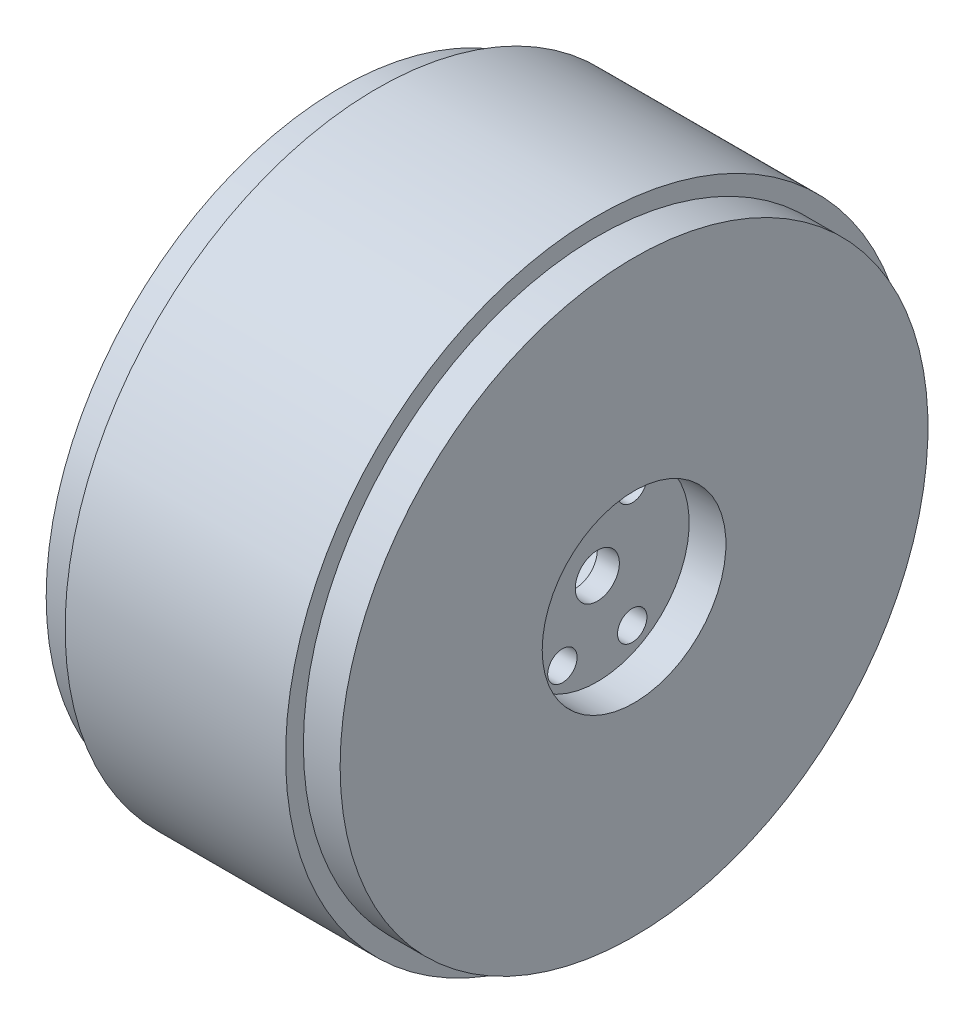
SolidWorks part; units mm, degrees
ref_plane "Plan de face" through (0, 0, 0) normal (0, 0, 1) x (1, 0, 0)
ref_plane "Plan de dessus" through (0, 0, 0) normal (0, 1, 0) x (1, 0, 0)
ref_plane "Plan de droite" through (0, 0, 0) normal (1, 0, 0) x (0, 0, -1)
sketch "Esquisse1" plane through (0, 0, 0) normal (0, 0, 1) x (1, 0, 0)
  line L0 (-49.6445, 0) -> (53.9199, 0) construction
  line L1 (0, 34) -> (0, 0)
  line L2 (0, 34) -> (-32, 34)
  line L3 (-32, 34) -> (-32, 40)
  line L4 (-32, 40) -> (-27, 40)
  line L5 (-27, 40) -> (-27, 39)
  line L6 (-27, 39) -> (3, 39)
  line L7 (3, 39) -> (3, 40)
  line L8 (3, 40) -> (8, 40)
  line L9 (8, 40) -> (8, 0)
  line L13 (0, 0) -> (8, 0)
  dimension "D2" = 5
  dimension "D3" = 5
  dimension "D4" = 40
  dimension "D5" = 1
  dimension "D6" = 8
  dimension "D10" = 6
  dimension "D11" = 1
  dimension "D12" = 30
revolve "Révolution1" add sketch "Esquisse1" angle 360 about L0
sketch "Esquisse2" plane through (0, 0, 0) normal (0, 0, 1) x (1, 0, 0)
  line L3 (0, 0) -> (8, 0) construction
  line L11 (8, -40) -> (8, 40) construction
  line L12 (8, 0) -> (8, 12.5)
  line L13 (8, 12.5) -> (3, 12.5)
  line L14 (3, 12.5) -> (3, 0)
  line L15 (3, 0) -> (8, 0)
  dimension "D1" = 25
  dimension "D2" = 5
revolve "Enlèvement de matière-Révolution1" cut sketch "Esquisse2" angle 360 about L3
sketch "Esquisse3" plane through (3, 0, 0) normal (1, 0, 0) x (0, 0, -1)
  line L0 (0, 12.5) -> (0, 0) construction
  line L1 (0, 0) -> (12.5, 0) construction
  line L2 (4.75, 8.2272) -> (0, 0) construction
  circle A0 centre (4.75, 8.2272) radius 2
  circle A2 centre (0, 0) radius 12.5 construction
  circle A3 centre (0, 0) radius 12.5 construction
  circle A4 centre (-4.75, 8.2272) radius 2
  circle A5 centre (4.75, -8.2272) radius 2
  circle A6 centre (-4.75, -8.2272) radius 2
  dimension "D1" = 4
  dimension "D2" = 9.5
  dimension "D3" = 30
extrude "Enlèv. mat.-Extru.1" cut sketch "Esquisse3" against normal through all
sketch "Esquisse4" plane through (3, 0, 0) normal (1, 0, 0) x (0, 0, -1)
  circle A0 centre (0, 0) radius 3
  dimension "D1" = 6
extrude "Enlèv. mat.-Extru.2" cut sketch "Esquisse4" against normal through all
sketch "Esquisse5" plane through (0, 0, 0) normal (0, 0, 1) x (1, 0, 0)
  line L0 (3, 39) -> (-27, 39) construction
  line L1 (3, 39) -> (-27, 39)
  line L2 (-27, 39) -> (-27, 42.4219)
  line L3 (-27, 42.4219) -> (3, 42.4219)
  line L4 (3, 42.4219) -> (3, 39)
  line L5 (0, 0) -> (-36.5095, 0) construction
revolve "Révolution2" add sketch "Esquisse5" angle 360 about L5
